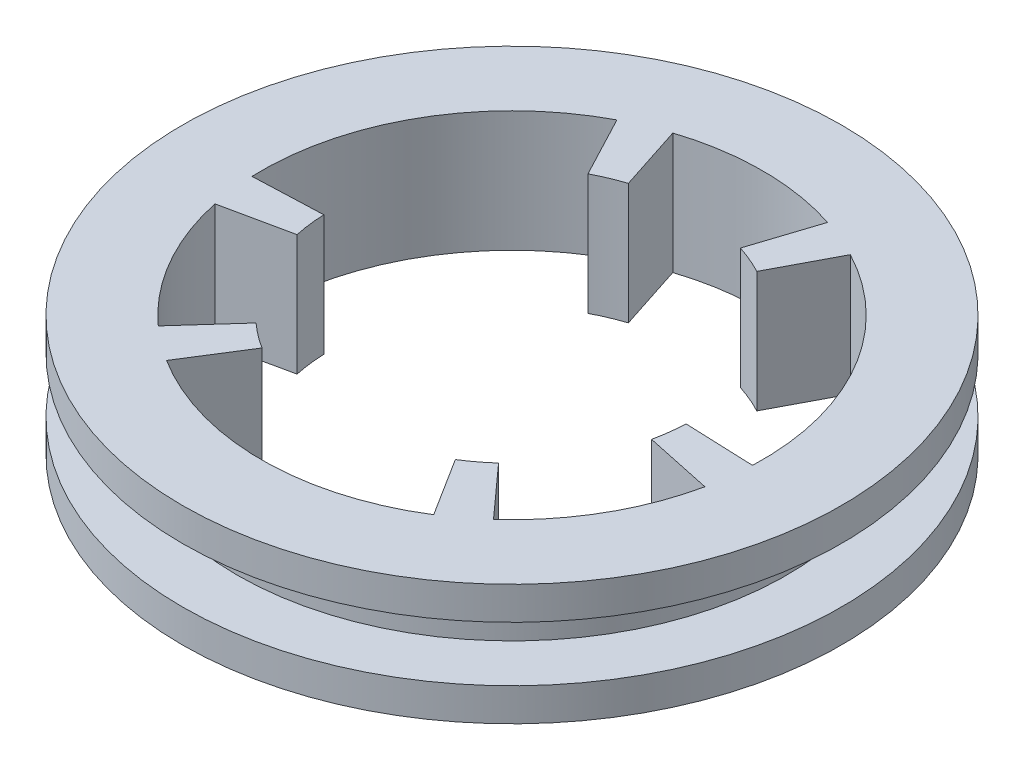
SolidWorks part; units mm, degrees
material "1060 Alloy"
ref_plane "Front Plane" through (0, 0, 0) normal (0, 0, 1) x (1, 0, 0)
ref_plane "Top Plane" through (0, 0, 0) normal (0, 1, 0) x (1, 0, 0)
ref_plane "Right Plane" through (0, 0, 0) normal (1, 0, 0) x (0, 0, -1)
sketch "Sketch2" plane through (0, 0, 0) normal (0, 0, 1) x (1, 0, 0)
  line L0 (0, 19.9874) -> (0, -21.8183) construction
  line L1 (0, -55) -> (0, 55) construction
  line L2 (-25, 2.5) -> (-25, -2.5)
  line L3 (55, 0) -> (-55, 0) construction
  line L4 (-25, 2.5) -> (-30, 2.5)
  line L5 (-30, 2.5) -> (-30, 5.5)
  line L6 (-30, 5.5) -> (0, 5.5)
  line L7 (-25, -2.5) -> (-30, -2.5)
  line L8 (-30, -2.5) -> (-30, -5.5)
  line L9 (-30, -5.5) -> (0, -5.5)
  line L10 (0, 5.5) -> (0, -5.5)
  point P7 (-25, 0)
  dimension "D1" = 5
  dimension "D2" = 5
  dimension "D3" = 3
  dimension "D4" = 3
  dimension "D5" = 25
revolve "Revolve1" add sketch "Sketch2" angle 360 about L0
sketch "Sketch3" plane through (0, 5.5, 0) normal (0, 1, 0) x (1, 0, 0)
  line L0 (0, 0) -> (30.2715, -17.4772) construction
  line L1 (0, -6.05) -> (0, 6.05) construction
  line L2 (22.3018, -4.7404) -> (16.1394, -3.4305)
  line L3 (15.2562, -16.9437) -> (11.0407, -12.2619)
  line L4 (-7.0456, 21.6841) -> (-5.0988, 15.6924)
  line L5 (-15.2562, -16.9437) -> (-11.0407, -12.2619)
  line L6 (-7.6876, 14.5997) -> (-10.6229, 20.1741)
  line L7 (-16.4875, -0.6422) -> (-22.7827, -0.8874)
  line L8 (-8.7999, -13.9575) -> (-12.1599, -19.2867)
  line L9 (8.7999, -13.9575) -> (12.1599, -19.2867)
  line L10 (-7.0456, 21.6841) -> (-5.0988, 15.6924) [skipped]
  line L11 (7.0456, 21.6841) -> (5.0988, 15.6924) [skipped]
  line L12 (-22.3018, -4.7404) -> (-16.1394, -3.4305) [skipped]
  line L13 (-22.3018, -4.7404) -> (-16.1394, -3.4305)
  line L14 (22.3018, -4.7404) -> (16.1394, -3.4305)
  line L15 (16.4875, -0.6422) -> (22.7827, -0.8874)
  line L16 (7.6876, 14.5997) -> (10.6229, 20.1741)
  line L17 (7.0456, 21.6841) -> (5.0988, 15.6924)
  circle A0 centre (0, 0) radius 22.8
  circle A1 centre (0, 0) radius 16.5
  circle A2 centre (0, -14) radius 8.8
  circle A5 centre (-12.1244, 7) radius 8.8
  circle A6 centre (12.1244, 7) radius 8.8
  point P15 (-0.0992, -0.0582)
  point P28 (0, 0)
  point P42 (0, 0)
  point P51 (0, 0)
  dimension "D1" = 45.6
  dimension "D2" = 33
  dimension "D4" = 3
  dimension "D3" = 60
  dimension "D5" = 14
  dimension "D7" = 36
  dimension "D8" = 3
extrude "Cut-Extrude1" cut sketch "Sketch3" against normal up to next
